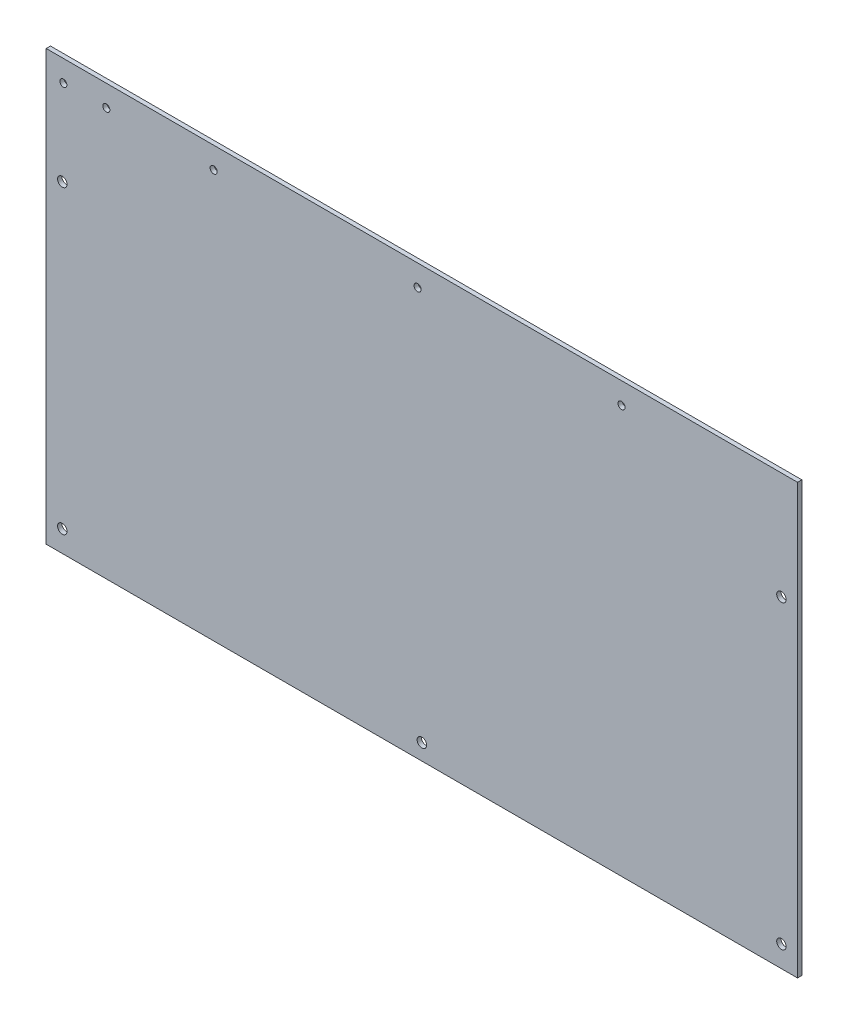
SolidWorks part; units mm, degrees
ref_plane "正面" through (0, 0, 0) normal (0, 0, 1) x (1, 0, 0)
ref_plane "平面" through (0, 0, 0) normal (0, 1, 0) x (1, 0, 0)
ref_plane "右側面" through (0, 0, 0) normal (1, 0, 0) x (0, 0, -1)
sketch "ｽｹｯﾁ1" plane through (0, 0, 0) normal (0, 0, 1) x (1, 0, 0)
  line L1 (-175, 100) -> (175, 100)
  line L2 (-175, 100) -> (-175, -100)
  line L3 (-175, -100) -> (175, -100)
  line L4 (175, 100) -> (175, -100)
  line L5 (-175, 100) -> (175, -100) construction
  line L6 (-175, -100) -> (175, 100) construction
  point P0 (0, 0)
  dimension "D1" = 350
  dimension "D2" = 200
extrude "ﾎﾞｽ - 押し出し1" add sketch "ｽｹｯﾁ1" along normal blind 2
sketch "ｽｹｯﾁ3" plane through (0, 0, 2) normal (0, 0, 1) x (1, 0, 0)
  line L0 (-167.5, -90) -> (-167.5, 50)
  line L1 (-175, -100) -> (-167.5, -100)
  line L2 (-175, -100) -> (-175, -90)
  line L3 (-175, -90) -> (-167.5, -90)
  line L4 (-167.5, -100) -> (-167.5, -90)
  line L5 (175, -100) -> (167.5, -100)
  line L6 (-175, -100) -> (175, -100) construction
  line L7 (167.5, -100) -> (167.5, -90)
  line L8 (167.5, -90) -> (167.5, 50)
  circle A0 centre (-167.5, 50) radius 2.2
  circle A1 centre (-167.5, -90) radius 2.2
  circle A2 centre (167.5, -90) radius 2.2
  circle A3 centre (167.5, 50) radius 2.2
  dimension "D7" = 4.4
  dimension "D8" = 4.4
  dimension "D9" = 4.4
  dimension "D10" = 4.4
  dimension "D1" = 7.5
  dimension "D2" = 10
  dimension "D3" = 140
  dimension "D4" = 7.5
  dimension "D5" = 10
  dimension "D6" = 140
extrude "ｶｯﾄ - 押し出し2" cut sketch "ｽｹｯﾁ3" against normal blind 160
sketch "ｽｹｯﾁ4" plane through (0, 0, 2) normal (0, 0, 1) x (1, 0, 0)
  line L0 (-175, -100) -> (-175, -92.5)
  line L1 (-175, 100) -> (-175, -100) construction
  line L2 (-175, -92.5) -> (175, -92.5)
  line L3 (175, -100) -> (175, 100) construction
  line L4 (-95, 90) -> (-95, -92.5)
  line L5 (0, 90) -> (0, -92.5)
  line L6 (95, 90) -> (95, -92.5)
  circle A0 centre (-95, -92.5) radius 2.2
  circle A1 centre (0, -92.5) radius 2.2
  circle A2 centre (95, -92.5) radius 2.2
  dimension "D2" = 4.4
  dimension "D3" = 4.4
  dimension "D4" = 4.4
  dimension "D1" = 7.5
extrude "ｶｯﾄ - 押し出し3" cut sketch "ｽｹｯﾁ4" against normal blind 160 contours L2 A1 | L2 A1 L5 | L5 A1 L2
sketch "ｽｹｯﾁ6" plane through (0, 0, 0) normal (0, 0, -1) x (-1, 0, 0)
  circle A0 centre (144.5942, 89.9813) radius 1.0967
  circle A1 centre (167, 89.9987) radius 1.0463
sketch "ｽｹｯﾁ9" plane through (0, 0, 2) normal (0, 0, 1) x (1, 0, 0)
  line L2 (-175, 100) -> (-175, -100) construction
  line L3 (-175, 90.0267) -> (-175, 100)
  line L4 (-175, 90.0267) -> (-97, 90.0267)
  line L5 (-97, 90.0267) -> (-2, 90.0267)
  line L6 (-2, 90.0267) -> (93, 90.0267)
  circle A0 centre (-97, 90.0267) radius 1.0922
  circle A1 centre (-2, 90.0267) radius 1.0812
  circle A2 centre (93, 90.0267) radius 1.0937
  dimension "D1" = 95
  dimension "D2" = 95
  dimension "D3" = 78
extrude "ｶｯﾄ - 押し出し6" cut sketch "ｽｹｯﾁ9" against normal blind 10
hole_wizard "M4x0.7 ねじ穴3" positions "3Dｽｹｯﾁ3" profile "ｽｹｯﾁ11" tap size "M4x0.7" standard "JIS" end condition through all
sketch3d "3Dｽｹｯﾁ3"
  line L0 (93, 90.0267, 0) -> (93, 90.0267, 2) construction
  line L1 (-2, 90.0267, 0) -> (-2, 90.0267, 2) construction
  line L2 (-97, 90.0267, 0) -> (-97, 90.0267, 2) construction
  point P0 (93, 90.0267, 2)
  point P4 (-2, 90.0267, 2)
  point P8 (-97, 90.0267, 2)
sketch "ｽｹｯﾁ11" plane through (93, 90.0267, 2) normal (1, 0, 0) x (0, -1, 0)
  line L0 (0, 0) -> (0, 2)
  line L1 (0, 2) -> (1.65, 2)
  line L2 (1.65, 2) -> (1.65, 0)
  line L5 (1.65, 0) -> (0, 0)
  line L11 (0, -6.35) -> (0, 107.95) construction
  dimension "次ｻｰﾌｪｽまでのねじ下穴ﾄﾞﾘﾙ直径" = 3.3
  dimension "次ｻｰﾌｪｽまでのねじ下穴ﾄﾞﾘﾙの深さ" = 2
cosmetic thread "穴のねじ山6" parameters "D2"=4
cosmetic thread "穴のねじ山7" parameters "D2"=4
cosmetic thread "穴のねじ山8" parameters "D2"=4
sketch "ｽｹｯﾁ12" plane through (0, 0, 2) normal (0, 0, 1) x (1, 0, 0)
  line L2 (-175, 100) -> (-175, -100) construction
  line L3 (-175, 90.0267) -> (-175, 100)
  line L4 (-175, 90.0267) -> (-167, 90.0267)
  line L5 (-167, 90.0267) -> (-147, 90.0267)
  circle A2 centre (-147, 90.0267) radius 1.0948
  circle A3 centre (-167, 90.0267) radius 0.6468
  dimension "D1" = 8
  dimension "D2" = 20
extrude "ｶｯﾄ - 押し出し7" cut sketch "ｽｹｯﾁ12" against normal blind 10
hole_wizard "M4x0.7 ねじ穴4" positions "3Dｽｹｯﾁ4" profile "ｽｹｯﾁ13" tap size "M4x0.7" standard "JIS" end condition through all
sketch3d "3Dｽｹｯﾁ4"
  line L0 (-147, 90.0267, 0) -> (-147, 90.0267, 2) construction
  line L1 (-167, 90.0267, 0) -> (-167, 90.0267, 2) construction
  point P0 (-147, 90.0267, 2)
  point P4 (-167, 90.0267, 2)
sketch "ｽｹｯﾁ13" plane through (-147, 90.0267, 2) normal (1, 0, 0) x (0, -1, 0)
  line L0 (0, 0) -> (0, 2)
  line L1 (0, 2) -> (1.65, 2)
  line L2 (1.65, 2) -> (1.65, 0)
  line L5 (1.65, 0) -> (0, 0)
  line L11 (0, -6.35) -> (0, 107.95) construction
  dimension "次ｻｰﾌｪｽまでのねじ下穴ﾄﾞﾘﾙ直径" = 3.3
  dimension "次ｻｰﾌｪｽまでのねじ下穴ﾄﾞﾘﾙの深さ" = 2
cosmetic thread "穴のねじ山9" parameters "D2"=4
cosmetic thread "穴のねじ山10" parameters "D2"=4
